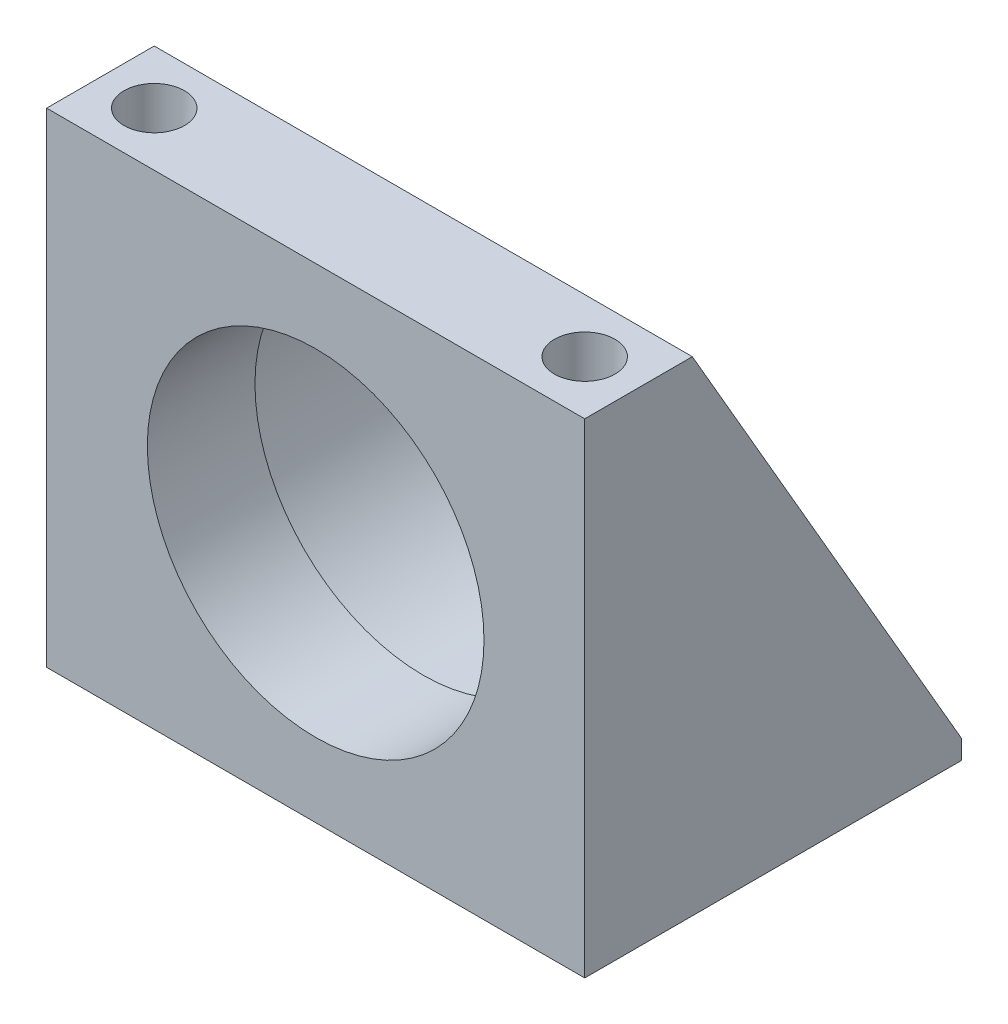
SolidWorks part; units mm, degrees
material "Alloy Steel"
ref_plane "Front Plane" through (0, 0, 0) normal (0, 0, 1) x (1, 0, 0)
ref_plane "Top Plane" through (0, 0, 0) normal (0, 1, 0) x (1, 0, 0)
ref_plane "Right Plane" through (0, 0, 0) normal (1, 0, 0) x (0, 0, -1)
sketch "Sketch1" plane through (0, 0, 0) normal (0, 0, 1) x (1, 0, 0)
  line L1 (-31.75, 57.15) -> (31.75, 57.15)
  line L2 (-31.75, 57.15) -> (-31.75, 0)
  line L3 (-31.75, 0) -> (31.75, 0)
  line L4 (31.75, 57.15) -> (31.75, 0)
  circle A0 centre (0, 28.575) radius 19.8628
  dimension "D4" = 39.7256
  dimension "D1" = 63.5
  dimension "D2" = 57.15
  dimension "D3" = 28.575
extrude "Extrude1" add sketch "Sketch1" against normal blind 44.45
sketch "Sketch2" plane through (31.75, 0, 0) normal (1, 0, 0) x (0, 0, -1)
  line L0 (12.7, 57.15) -> (44.45, 2.286)
  line L1 (0, 0) -> (0, 57.15) construction
  line L2 (44.45, 0) -> (0, 0) construction
  line L4 (0, 57.15) -> (0, 0)
  line L5 (0, 0) -> (44.45, 0)
  line L6 (44.45, 0) -> (44.45, 57.15)
  line L7 (44.45, 57.15) -> (0, 57.15)
  line L10 (44.45, 2.286) -> (44.45, 57.15)
  line L11 (44.45, 57.15) -> (12.7, 57.15)
  dimension "D2" = 12.7
  dimension "D3" = 2.286
  dimension "D1" = 0
extrude "Cut-Extrude1" cut sketch "Sketch2" against normal through all
sketch "Sketch3" plane through (0, 0, -44.45) normal (0, 0, -1) x (-1, 0, 0)
  circle A0 centre (0, 28.575) radius 22.225
  dimension "D1" = 44.45
extrude "Cut-Extrude2" cut sketch "Sketch3" against normal offset from surface (31.75 mm away) 12.7 up to face at (19.8628, 28.575, 0)
fillet "Fillet1" radius 1.524 1 edges at (22.225, 28.575, -12.7)
hole_wizard "Hole1" positions "Sketch5" profile "Sketch4" legacy end condition up to next
sketch "Sketch5" plane through (0, 57.15, 0) normal (0, 1, 0) x (-1, 0, 0)
  line L0 (-31.75, -12.7) -> (-31.75, 0) construction
  line L1 (-31.75, 0) -> (31.75, 0) construction
  point P0 (25.4, -6.35)
  point P1 (-25.4, -6.35)
  dimension "D1" = 6.35
  dimension "D2" = 6.35
  dimension "D3" = 50.8
sketch "Sketch4" plane through (-25.4, 57.15, -6.35) normal (1, 0, 0) x (0, 0, 1)
  line L0 (0, 0) -> (0, 57.15)
  line L1 (0, 57.15) -> (3.5687, 57.15)
  line L2 (3.5687, 57.15) -> (3.5687, 0)
  line L3 (3.5687, 0) -> (0, 0)
  line L4 (0, 110) -> (0, -10) construction
  dimension "Diameter" = 7.1374
  dimension "Depth" = 57.15
